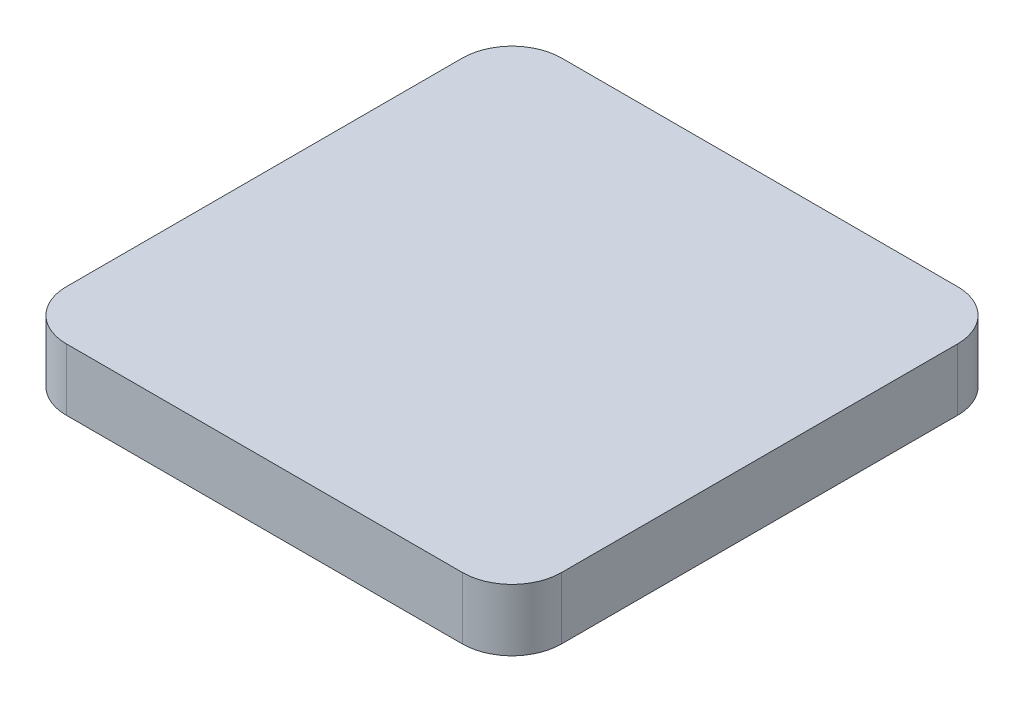
SolidWorks part; units mm, degrees
ref_plane "Front Plane" through (0, 0, 0) normal (0, 0, 1) x (1, 0, 0)
ref_plane "Top Plane" through (0, 0, 0) normal (0, 1, 0) x (1, 0, 0)
ref_plane "Right Plane" through (0, 0, 0) normal (1, 0, 0) x (0, 0, -1)
sketch "Sketch1" plane through (0, 0, 0) normal (0, 1, 0) x (1, 0, 0)
  line L1 (-12.7, 12.7) -> (12.7, 12.7)
  line L2 (-12.7, 12.7) -> (-12.7, -12.7)
  line L3 (-12.7, -12.7) -> (12.7, -12.7)
  line L4 (12.7, 12.7) -> (12.7, -12.7)
  line L5 (-12.7, 12.7) -> (12.7, -12.7) construction
  line L6 (-12.7, -12.7) -> (12.7, 12.7) construction
  point P0 (0, 0)
  dimension "D1" = 25.4
  dimension "D2" = 25.4
extrude "Boss-Extrude1" add sketch "Sketch1" along normal blind 3.175
fillet "Fillet1" radius 2.54 4 edges at (12.7, 1.5875, -12.7) (-12.7, 1.5875, -12.7) (-12.7, 1.5875, 12.7) (12.7, 1.5875, 12.7)
